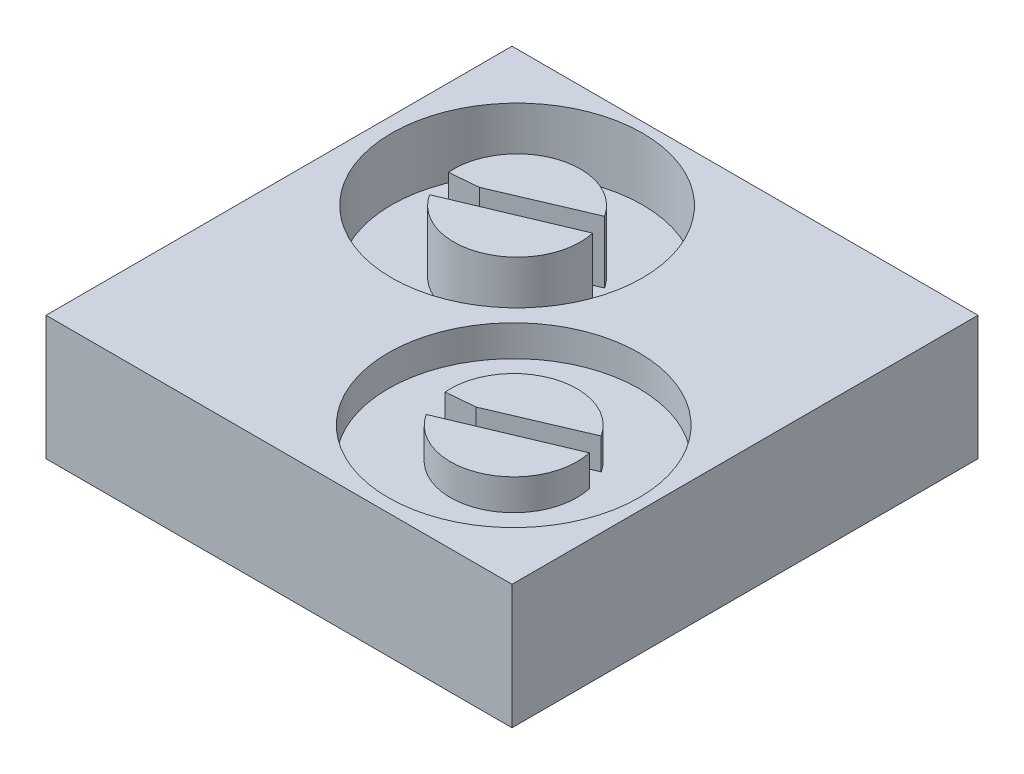
SolidWorks part; units mm, degrees
ref_plane "Front Plane" through (0, 0, 0) normal (0, 0, 1) x (1, 0, 0)
ref_plane "Top Plane" through (0, 0, 0) normal (0, 1, 0) x (1, 0, 0)
ref_plane "Right Plane" through (0, 0, 0) normal (1, 0, 0) x (0, 0, -1)
sketch "Sketch1" plane through (0, 0, 0) normal (0, 1, 0) x (1, 0, 0)
  line L1 (-10.5923, 10.5378) -> (4.4077, 10.5378)
  line L2 (-10.5923, 10.5378) -> (-10.5923, -4.4622)
  line L3 (-10.5923, -4.4622) -> (4.4077, -4.4622)
  line L4 (4.4077, 10.5378) -> (4.4077, -4.4622)
  line L5 (-10.5923, 10.5378) -> (4.4077, -4.4622) construction
  line L6 (-10.5923, -4.4622) -> (4.4077, 10.5378) construction
  point P4 (-3.0923, 3.0378)
  dimension "D1" = 15
  dimension "D2" = 15
extrude "Boss-Extrude1" add sketch "Sketch1" along normal blind 4
sketch "Sketch2" plane through (0, 4, 0) normal (0, 1, 0) x (1, 0, 0)
  line L1 (-8.0999, 5.9998) -> (-7.1799, 6.081)
  line L2 (-7.1799, 6.081) -> (-4.3602, 7.2862)
  line L3 (-4.0826, 6.6257) -> (-6.2537, 5.7111)
  line L4 (-6.2537, 5.7111) -> (-7.7801, 5.0708)
  circle A0 centre (-6.0704, 6.179) radius 4.0374
  arc A1 (-7.7801, 5.0708) -> (-4.0826, 6.6257) centre (-6.0704, 6.179) ccw
  arc A3 (-4.3602, 7.2862) -> (-8.0999, 5.9998) centre (-6.0704, 6.179) ccw
  point P2 (-5.2937, 4.6526)
  point P3 (-5.7749, 3.6248)
  point P4 (0, 0)
  dimension "D1" = 2
sketch "Sketch3" plane through (0, 4, 0) normal (0, 1, 0) x (1, 0, 0)
  line L0 (-2.0295, -0.1792) -> (-1.1094, -0.098)
  line L1 (-1.1094, -0.098) -> (1.7103, 1.1072)
  line L2 (1.9878, 0.4467) -> (-0.1833, -0.4679)
  line L3 (-0.1833, -0.4679) -> (-1.7096, -1.1082)
  circle A0 centre (0, 0) radius 4.0374
  arc A1 (-1.7096, -1.1082) -> (1.9878, 0.4467) centre (0, 0) ccw
  arc A2 (1.7103, 1.1072) -> (-2.0295, -0.1792) centre (0, 0) ccw
extrude "Cut-Extrude2" cut sketch "Sketch3" against normal blind 1
extrude "Cut-Extrude3" cut sketch "Sketch2" against normal blind 2
equation "\"15צצ\"=4.51775"
